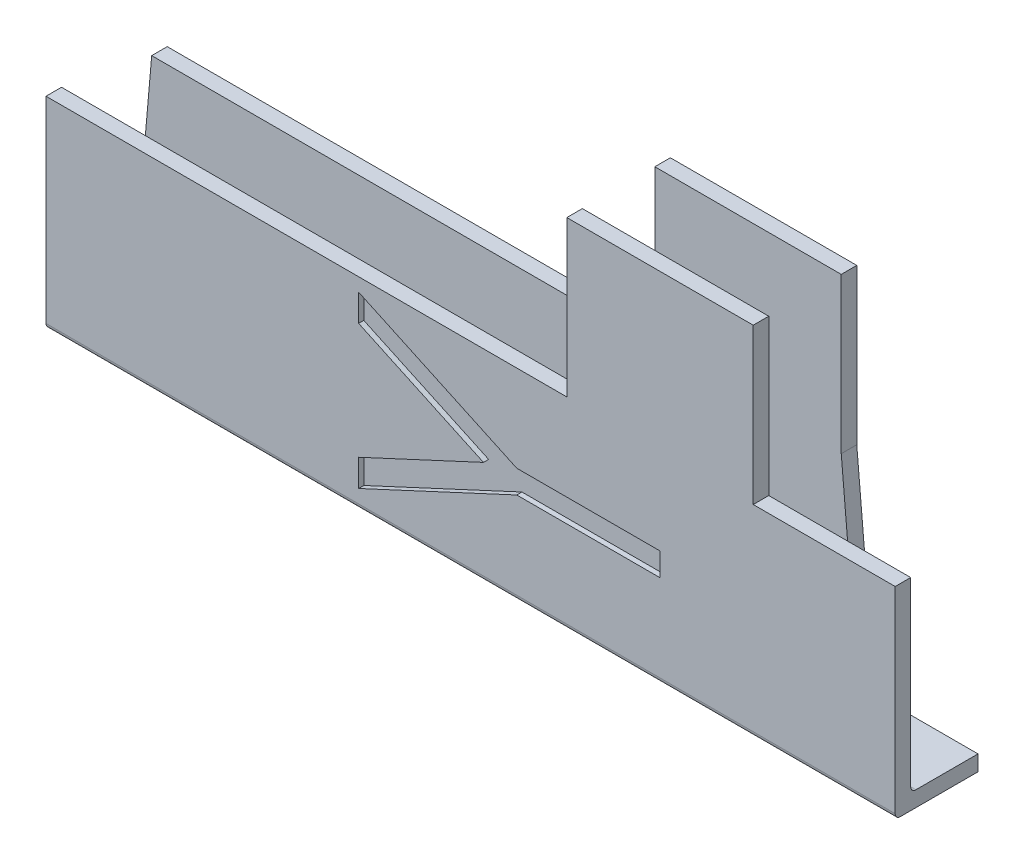
SolidWorks part; units mm, degrees
ref_plane "Front" through (0, 0, 0) normal (0, 0, 1) x (1, 0, 0)
ref_plane "Top" through (0, 0, 0) normal (0, 1, 0) x (1, 0, 0)
ref_plane "Right" through (0, 0, 0) normal (1, 0, 0) x (0, 0, -1)
sketch "Çizim1" plane through (0, 0, 0) normal (0, 0, 1) x (1, 0, 0)
  line L1 (-35, 9.75) -> (35, 9.75)
  line L2 (-35, 9.75) -> (-35, -9.75)
  line L3 (-35, -9.75) -> (35, -9.75)
  line L4 (35, 9.75) -> (35, -9.75)
  line L5 (-35, 9.75) -> (35, -9.75) construction
  line L6 (-35, -9.75) -> (35, 9.75) construction
  point P0 (0, 0)
  dimension "D1" = 19.5
  dimension "D2" = 70
extrude "Yükseklik-Ekstrüzyon1" add sketch "Çizim1" along normal blind 10
shell "İç Boşaltma1" thickness 1.5
fillet "Radyus1" radius 0.5 2 edges at (0, -8.25, 1.5) (0, -8.25, 8.5)
fillet "Radyus2" radius 0.5 2 edges at (0, -9.75, 0) (0, -9.75, 10)
sketch "Çizim2" plane through (0, 0, 0) normal (0, 0, -1) x (-1, 0, 0)
  line L0 (35, -9.75) -> (33.294, 9.75)
  line L1 (-35, 9.75) -> (35, 9.75) construction
  line L2 (33.294, 9.75) -> (35, 9.75)
  line L3 (35, 9.75) -> (35, -9.75)
  dimension "D1" = 5
extrude "Kes-Ekstrüzyon1" cut sketch "Çizim2" against normal blind 2
mirror "Aynalama1" about plane through (0, 0, 0) normal (1, 0, 0) of "Kes-Ekstrüzyon1"
sketch "Çizim7" plane through (-35, 0, 0) normal (-1, 0, 0) x (0, 0, 1)
  line L6 (2, -8.25) -> (2, -9.75)
  line L7 (2, -9.75) -> (9.5, -9.75)
  line L8 (10, -9.25) -> (10, 9.75)
  line L9 (10, 9.75) -> (8.5, 9.75)
  line L10 (8.5, 9.75) -> (8.5, -7.75)
  line L11 (8, -8.25) -> (2, -8.25)
  line L12 (2, -8.25) -> (2, -9.75)
  line L13 (2, -9.75) -> (9.5, -9.75)
  line L14 (10, -9.25) -> (10, 9.75)
  line L15 (10, 9.75) -> (8.5, 9.75)
  line L16 (8.5, 9.75) -> (8.5, -7.75)
  line L17 (8, -8.25) -> (2, -8.25)
  arc A3 (9.5, -9.75) -> (10, -9.25) centre (9.5, -9.25) ccw
  arc A4 (8, -8.25) -> (8.5, -7.75) centre (8, -7.75) ccw
  arc A6 (9.5, -9.75) -> (10, -9.25) centre (9.5, -9.25) ccw
  arc A7 (8, -8.25) -> (8.5, -7.75) centre (8, -7.75) ccw
  dimension "D1" = 0
extrude "Yükseklik-Ekstrüzyon3" add sketch "Çizim7" along normal blind 10
sketch "Çizim8" plane through (0, 9.75, 0) normal (0, 1, 0) x (1, 0, 0)
  line L0 (-15.294, 0) -> (-15.294, -1.5)
  line L1 (-15.294, -8.5) -> (-15.294, -10)
  line L2 (-33.294, -8.5) -> (-33.294, -10)
  line L4 (33.294, -1.5) -> (33.294, 0)
  line L5 (33.294, 0) -> (-33.294, 0)
  line L6 (-33.294, 0) -> (-33.294, -1.5)
  line L7 (-33.294, -1.5) -> (33.294, -1.5)
  line L9 (-15.294, 0) -> (-33.294, 0)
  line L10 (-33.294, 0) -> (-33.294, -1.5)
  line L11 (-33.294, -1.5) -> (-15.294, -1.5)
  line L12 (35, -10) -> (35, -8.5)
  line L13 (35, -8.5) -> (-45, -8.5)
  line L14 (-45, -8.5) -> (-45, -10)
  line L15 (-45, -10) -> (35, -10)
  line L17 (-15.294, -8.5) -> (-33.294, -8.5)
  line L19 (-33.294, -10) -> (-15.294, -10)
  dimension "D3" = 18
  dimension "D1" = 0
  dimension "D2" = 0
extrude "Yükseklik-Ekstrüzyon4" add sketch "Çizim8" along normal blind 15
mirror "Aynalama3" about plane through (0, 0, 0) normal (1, 0, 0) of "Yükseklik-Ekstrüzyon3", "Yükseklik-Ekstrüzyon4"
sketch "Çizim9" plane through (-45, 0, 0) normal (-1, 0, 0) x (0, 0, 1)
  line L6 (2, -9.75) -> (9.5, -9.75)
  line L7 (10, -9.25) -> (10, 9.75)
  line L8 (10, 9.75) -> (8.5, 9.75)
  line L9 (8.5, 9.75) -> (8.5, -7.75)
  line L10 (8, -8.25) -> (2, -8.25)
  line L11 (2, -8.25) -> (2, -9.75)
  line L12 (2, -9.75) -> (9.5, -9.75)
  line L13 (10, -9.25) -> (10, 9.75)
  line L14 (10, 9.75) -> (8.5, 9.75)
  line L15 (8.5, 9.75) -> (8.5, -7.75)
  line L16 (8, -8.25) -> (2, -8.25)
  line L17 (2, -8.25) -> (2, -9.75)
  arc A2 (9.5, -9.75) -> (10, -9.25) centre (9.5, -9.25) ccw
  arc A3 (8, -8.25) -> (8.5, -7.75) centre (8, -7.75) ccw
  arc A4 (9.5, -9.75) -> (10, -9.25) centre (9.5, -9.25) ccw
  arc A5 (8, -8.25) -> (8.5, -7.75) centre (8, -7.75) ccw
  dimension "D1" = 0
extrude "Kes-Ekstrüzyon3" cut sketch "Çizim9" against normal blind 10
sketch "Çizim10" plane through (-33.294, 0, 0) normal (-1, 0, 0) x (0, 0, 1)
  line L0 (0, 9.75) -> (1.5, 9.75) construction
  line L1 (1.5, 9.75) -> (1.5, 24.75) construction
  line L2 (1.5, 24.75) -> (0, 24.75) construction
  line L3 (0, 24.75) -> (0, 9.75) construction
  line L4 (8.5, 9.75) -> (10, 9.75) construction
  line L5 (10, 9.75) -> (10, 24.75) construction
  line L6 (10, 24.75) -> (8.5, 24.75) construction
  line L7 (8.5, 24.75) -> (8.5, 9.75) construction
  line L8 (0, 9.75) -> (1.5, 9.75)
  line L9 (1.5, 9.75) -> (1.5, 24.75)
  line L10 (1.5, 24.75) -> (0, 24.75)
  line L11 (0, 24.75) -> (0, 9.75)
  line L12 (8.5, 9.75) -> (10, 9.75)
  line L13 (10, 9.75) -> (10, 24.75)
  line L14 (10, 24.75) -> (8.5, 24.75)
  line L15 (8.5, 24.75) -> (8.5, 9.75)
extrude "Kes-Ekstrüzyon4" cut sketch "Çizim10" against normal up to surface (18 mm away) up to face at (-15.294, 17.25, 9.25)
sketch "Çizim11" plane through (0, 0, 10) normal (0, 0, 1) x (1, 0, 0)
  line L0 (24.294, 9.75) -> (24.294, -9.25) construction
  line L2 (-35, -9.25) -> (45, -9.25) construction
  line L3 (15.294, 9.75) -> (33.294, 9.75) construction
  text T0 "Y" font "Century Gothic" height in points 110
extrude "Kes-Ekstrüzyon5" cut sketch "Çizim11" against normal blind 0.5
ref_plane "Düzlem2" through (0, 0, 5) normal (0, 0, 1) x (1, 0, 0)
mirror "Aynalama4" about plane through (0, 0, 5) normal (0, 0, 1) of "Kes-Ekstrüzyon5"
sketch "Çizim12" plane through (45, 0, 0) normal (1, 0, 0) x (0, 0, -1)
  line L6 (-9.5, -9.75) -> (-2, -9.75)
  line L7 (-2, -9.75) -> (-2, -8.25)
  line L8 (-2, -8.25) -> (-8, -8.25)
  line L9 (-8.5, -7.75) -> (-8.5, 9.75)
  line L10 (-8.5, 9.75) -> (-10, 9.75)
  line L11 (-10, 9.75) -> (-10, -9.25)
  line L12 (-9.5, -9.75) -> (-2, -9.75)
  line L13 (-2, -9.75) -> (-2, -8.25)
  line L14 (-2, -8.25) -> (-8, -8.25)
  line L15 (-8.5, -7.75) -> (-8.5, 9.75)
  line L16 (-8.5, 9.75) -> (-10, 9.75)
  line L17 (-10, 9.75) -> (-10, -9.25)
  arc A2 (-8.5, -7.75) -> (-8, -8.25) centre (-8, -7.75) ccw
  arc A3 (-10, -9.25) -> (-9.5, -9.75) centre (-9.5, -9.25) ccw
  arc A4 (-8.5, -7.75) -> (-8, -8.25) centre (-8, -7.75) ccw
  arc A5 (-10, -9.25) -> (-9.5, -9.75) centre (-9.5, -9.25) ccw
  dimension "D1" = 0
extrude "Yükseklik-Ekstrüzyon5" add sketch "Çizim12" along normal blind 2
